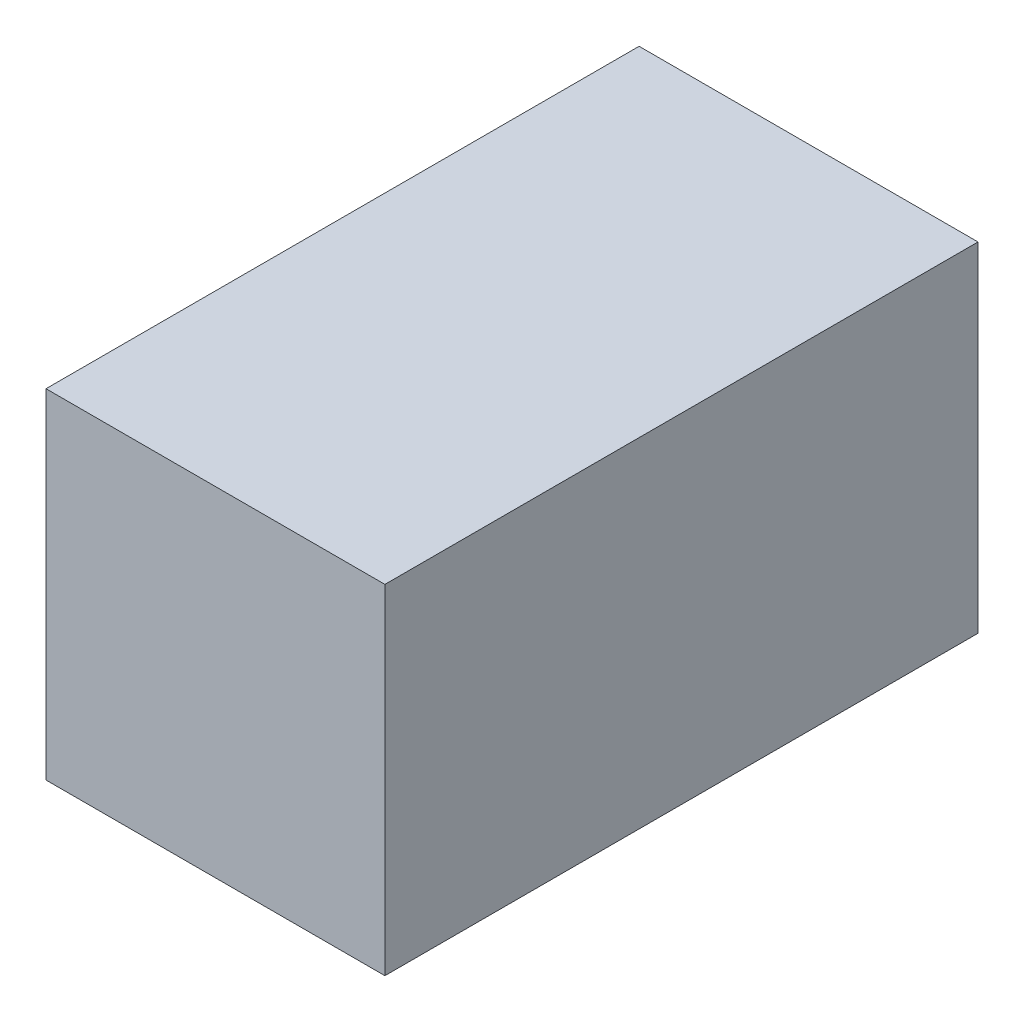
SolidWorks part; units mm, degrees
other "COLL.BOX-Boss-Extrude2"
ref_plane "Front Plane" through (0, 0, 0) normal (0, 0, 1) x (1, 0, 0)
ref_plane "Top Plane" through (0, 0, 0) normal (0, 1, 0) x (1, 0, 0)
ref_plane "Right Plane" through (0, 0, 0) normal (1, 0, 0) x (0, 0, -1)
sketch "Sketch1" plane through (0, 0, 0) normal (0, 0, 1) x (1, 0, 0)
  line L1 (-19.05, 25.5512) -> (31.75, 25.5512)
  line L2 (-19.05, 25.5512) -> (-19.05, -25.2488)
  line L3 (-19.05, -25.2488) -> (31.75, -25.2488)
  line L4 (31.75, 25.5512) -> (31.75, -25.2488)
  dimension "D1" = 50.8
  dimension "D2" = 50.8
extrude "Boss-Extrude1" add sketch "Sketch1" along normal blind 88.9
sketch "Sketch2" plane through (0, 0, 88.9) normal (0, 0, 1) x (1, 0, 0)
  line L1 (-19.05, 25.5512) -> (31.75, 25.5512)
  line L2 (-19.05, 25.5512) -> (-19.05, -25.2488)
  line L3 (-19.05, -25.2488) -> (31.75, -25.2488)
  line L4 (31.75, 25.5512) -> (31.75, -25.2488)
extrude "Boss-Extrude2" add sketch "Sketch2" against normal up to surface (88.9 mm away) separate body up to face at (6.35, 0.1512, 0)
sketch "Sketch3" plane through (0, 0, 0) normal (0, 0, -1) x (-1, 0, 0)
  line L0 (-6.35, 25.5512) -> (-6.35, 0.1512)
  line L1 (19.05, 25.5512) -> (-31.75, 25.5512) construction
  line L3 (-6.35, 0.1512) -> (19.05, 0.1512)
  line L5 (19.05, -25.2488) -> (19.05, 25.5512) construction
